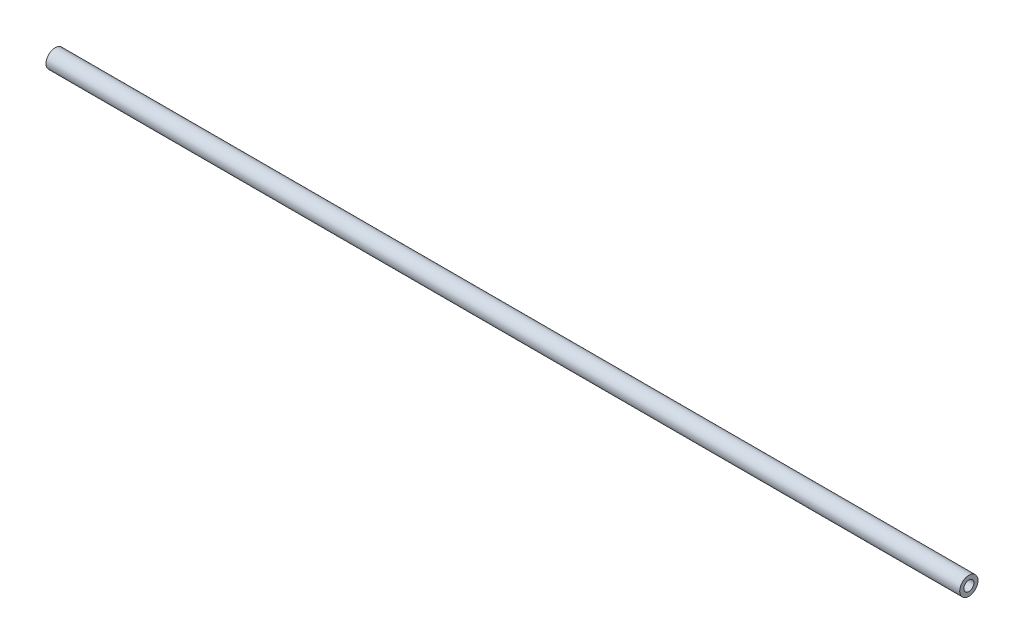
SolidWorks part; units mm, degrees
material "Alloy Steel"
ref_plane "Front Plane" through (0, 0, 0) normal (0, 0, 1) x (1, 0, 0)
ref_plane "Top Plane" through (0, 0, 0) normal (0, 1, 0) x (1, 0, 0)
ref_plane "Right Plane" through (0, 0, 0) normal (1, 0, 0) x (0, 0, -1)
sketch "Sketch1" plane through (0, 0, 0) normal (1, 0, 0) x (0, 0, -1)
  circle A0 centre (0, 0) radius 3
  dimension "D1" = 6
extrude "Boss-Extrude1" add sketch "Sketch1" along normal blind 300
hole_wizard "M4 Tapped Hole2" positions "3DSketch2" profile "Sketch3" tap size "M4" standard "ISO"
sketch3d "3DSketch2"
  line L0 (300, 0, 0) -> (0, 0, 0) construction
  circle A0 centre (0, 0, 0) radius 3 construction
  point P0 (-2.0188, -0.8012, -0.056)
  point P3 (0, 0, 0)
  point P5 (0, 0, 0)
  point P7 (300, 0, 0)
  point P15 (3, 0, 0)
sketch "Sketch3" plane through (0, 0, 0) normal (0, 1, 0) x (0, 0, 1)
  line L0 (0, 0) -> (0, 11.0914)
  line L1 (0, 11.0914) -> (1.65, 10.1)
  line L2 (1.65, 10.1) -> (1.65, 0)
  line L5 (1.65, 0) -> (0, 0)
  line L10 (0, 11.0914) -> (-1.65, 10.1) construction
  line L11 (0, -6.35) -> (0, 107.95) construction
  dimension "Tap Drill Dia." = 3.3
  dimension "Tap Drill Depth" = 10.1
  dimension "Drill Angle" = 118
cosmetic thread "Hole Thread3" parameters "D1"=8, "D2"=4
cosmetic thread "Hole Thread4" parameters "D1"=8, "D2"=4
cosmetic thread "Hole Thread5" parameters "D1"=8, "D2"=4
cosmetic thread "Hole Thread6" parameters "D1"=8, "D2"=4
